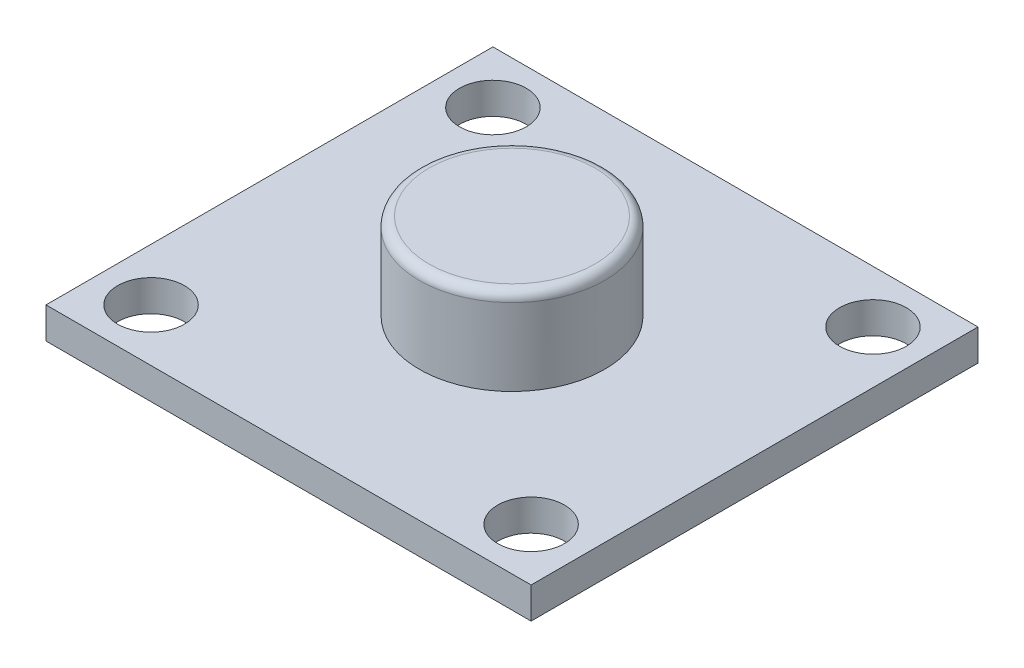
SolidWorks part; units mm, degrees
ref_plane "Front Plane" through (0, 0, 0) normal (0, 0, 1) x (1, 0, 0)
ref_plane "Top Plane" through (0, 0, 0) normal (0, 1, 0) x (1, 0, 0)
ref_plane "Right Plane" through (0, 0, 0) normal (1, 0, 0) x (0, 0, -1)
sketch "Sketch1" plane through (0, 0, 0) normal (0, 1, 0) x (1, 0, 0)
  line L1 (-12.7, -11.7) -> (12.7, -11.7)
  line L2 (-12.7, -11.7) -> (-12.7, 11.7)
  line L3 (-12.7, 11.7) -> (12.7, 11.7)
  line L4 (12.7, -11.7) -> (12.7, 11.7)
  line L5 (-12.7, -11.7) -> (12.7, 11.7) construction
  line L6 (-12.7, 11.7) -> (12.7, -11.7) construction
  point P0 (0, 0)
  dimension "D1" = 25.4
  dimension "D2" = 23.4
extrude "Boss-Extrude1" add sketch "Sketch1" along normal blind 1.64
sketch "Sketch2" plane through (0, 1.64, 0) normal (0, 1, 0) x (1, 0, 0)
  line L0 (-12.7, 11.7) -> (-12.7, 10.7) construction
  line L1 (-12.7, 11.7) -> (-12.7, -11.7) construction
  line L2 (-12.7, 10.7) -> (12.7, 10.7) construction
  line L3 (12.7, -11.7) -> (12.7, 11.7) construction
  line L4 (-12.7, -11.7) -> (-12.7, -10.7) construction
  line L5 (-12.7, -10.7) -> (-12.7, -11.7) construction
  line L6 (-12.7, -11.7) -> (12.7, -11.7) construction
  line L7 (-12.7, -11.7) -> (-11.7, -11.7) construction
  line L8 (-12.7, -10.7) -> (12.7, -10.7) construction
  line L9 (-11.7, -11.7) -> (-11.7, 11.7) construction
  line L10 (12.7, 11.7) -> (-12.7, 11.7) construction
  line L11 (12.7, -11.7) -> (11.7, -11.7) construction
  line L12 (11.7, -11.7) -> (11.7, 11.7) construction
  line L13 (-11.7, 10.7) -> (-11.7, 8.95) construction
  line L14 (-11.7, 10.7) -> (-9.95, 10.7) construction
  line L15 (-9.95, 10.7) -> (-9.95, 8.95) construction
  line L16 (11.7, 10.7) -> (9.95, 10.7) construction
  line L17 (9.95, 10.7) -> (9.95, 8.95) construction
  line L18 (9.95, 8.95) -> (11.7, 8.95) construction
  line L19 (11.7, -10.7) -> (11.7, -8.95) construction
  line L20 (11.7, -8.95) -> (9.95, -8.95) construction
  line L21 (9.95, -8.95) -> (9.95, -10.7) construction
  line L22 (9.95, -10.7) -> (11.7, -10.7) construction
  line L23 (-11.7, -10.7) -> (-11.7, -8.95) construction
  line L24 (-11.7, -8.95) -> (-9.95, -8.95) construction
  line L25 (-9.95, -8.95) -> (-9.95, -10.7) construction
  circle A0 centre (-9.95, -8.95) radius 1.75
  circle A1 centre (9.95, -8.95) radius 1.75
  circle A2 centre (9.95, 8.95) radius 1.75
  circle A3 centre (-9.95, 8.95) radius 1.75
extrude "Cut-Extrude1" cut sketch "Sketch2" against normal through all
sketch "Sketch3" plane through (0, 1.64, 0) normal (0, 1, 0) x (1, 0, 0)
  line L0 (-12.7, 0) -> (12.7, 0) construction
  line L1 (-12.7, 11.7) -> (-12.7, -11.7) construction
  line L2 (12.7, -11.7) -> (12.7, 11.7) construction
  line L4 (0, 0) -> (0, 11.7) construction
  line L5 (12.7, 11.7) -> (-12.7, 11.7) construction
  circle A0 centre (0, 0) radius 4.85
extrude "Boss-Extrude2" add sketch "Sketch3" along normal blind 4.53 contours A0
fillet "Fillet1" radius 0.5 1 edges at (0, 6.17, 4.85)
sketch "Sketch4" plane through (0, 1.64, 0) normal (0, 1, 0) x (1, 0, 0)
  line L0 (-12.7, 0) -> (12.7, 0)
  line L1 (-12.7, 11.7) -> (-12.7, -11.7) construction
  line L2 (12.7, -11.7) -> (12.7, 11.7) construction
  line L3 (12.7, 0) -> (0, 11.7)
  line L4 (12.7, 11.7) -> (-12.7, 11.7) construction
  line L5 (0, 11.7) -> (0, 0)
